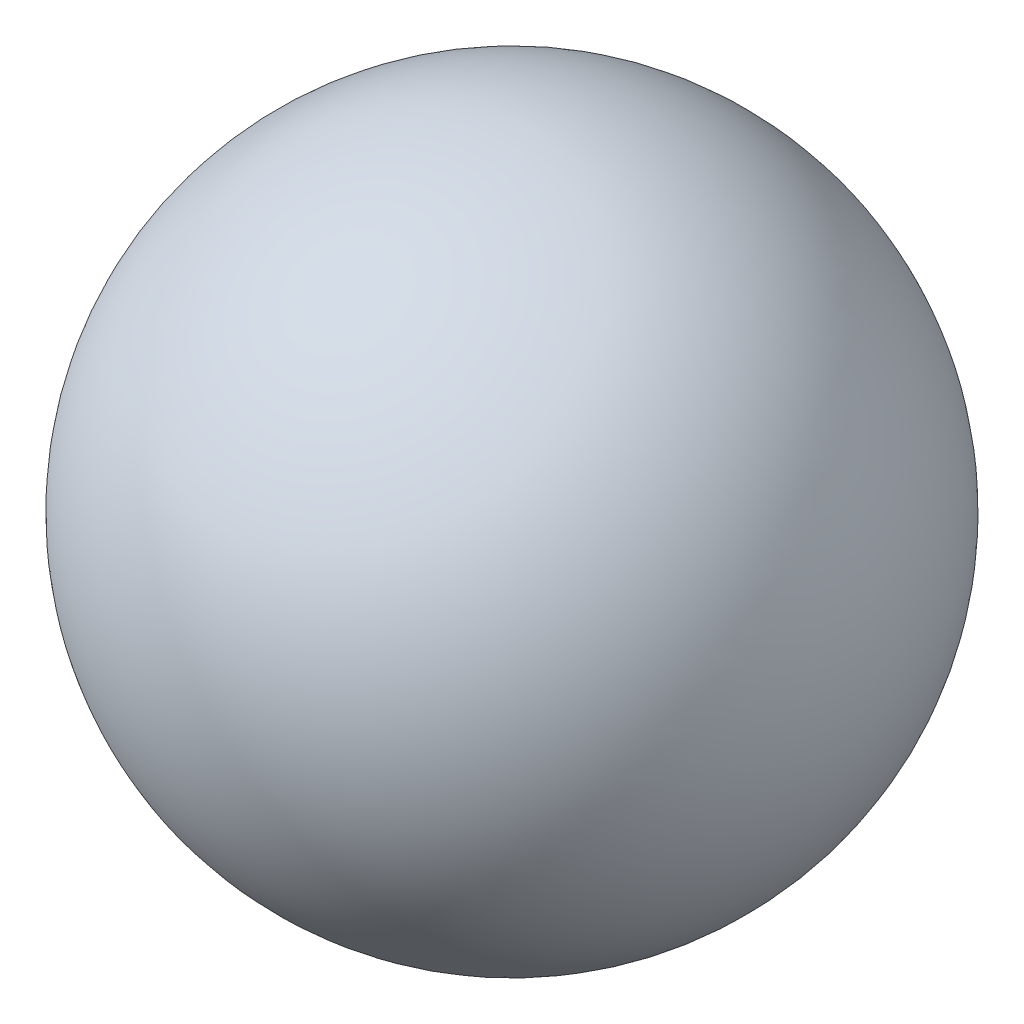
SolidWorks part; units mm, degrees
ref_plane "Front Plane" through (0, 0, 0) normal (0, 0, 1) x (1, 0, 0)
ref_plane "Top Plane" through (0, 0, 0) normal (0, 1, 0) x (1, 0, 0)
ref_plane "Right Plane" through (0, 0, 0) normal (1, 0, 0) x (0, 0, -1)
sketch "Sketch1" plane through (0, 0, 0) normal (0, 1, 0) x (1, 0, 0)
  line L0 (0, 44.4429) -> (0, -44.4429)
  arc A0 (0, -44.4429) -> (0, 44.4429) centre (0, 0) ccw
  dimension "D1" = 88.8857
revolve "Revolve1" add sketch "Sketch1" angle 360 about L0
